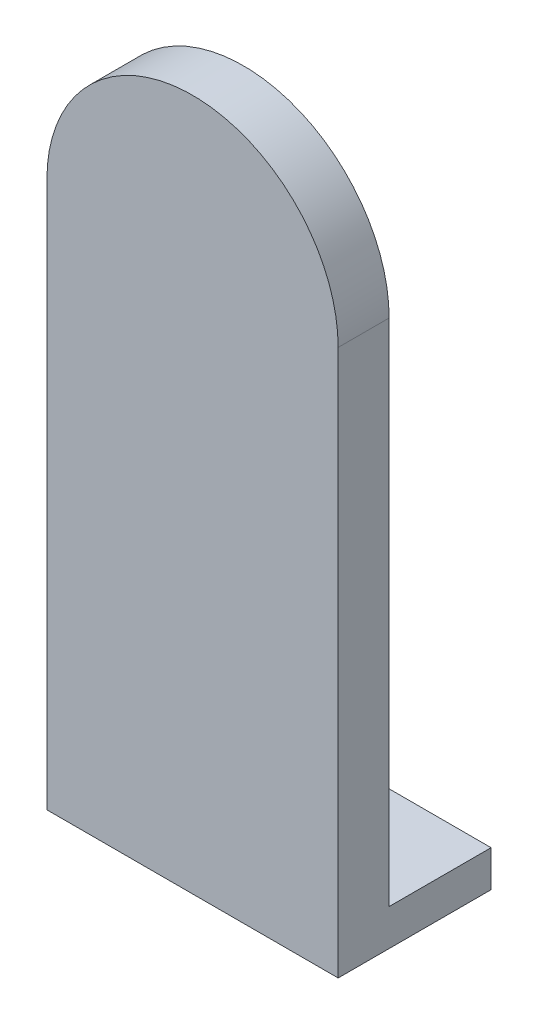
SolidWorks part; units mm, degrees
material "PBT General Purpose"
ref_plane "Front" through (0, 0, 0) normal (0, 0, 1) x (1, 0, 0)
ref_plane "Top" through (0, 0, 0) normal (0, 1, 0) x (1, 0, 0)
ref_plane "Right" through (0, 0, 0) normal (1, 0, 0) x (0, 0, -1)
sketch "Sketch1" plane through (0, 0, 0) normal (0, 0, 1) x (1, 0, 0)
  line L0 (0, 0) -> (0, -75) construction
  line L1 (20, 0) -> (20, -75)
  line L2 (-20, 0) -> (-20, -75)
  line L3 (-20, -75) -> (20, -75)
  arc A0 (20, 0) -> (-20, 0) centre (0, 0) ccw
  point P3 (0, -37.5)
  dimension "D1" = 40
  dimension "D2" = 75
extrude "Boss-Extrude1" add sketch "Sketch1" along normal blind 7
sketch "Sketch2" plane through (0, 0, 0) normal (0, 0, -1) x (-1, 0, 0)
  circle A0 centre (0, 0) radius 5
  dimension "D1" = 10
extrude "Boss-Extrude2" add sketch "Sketch2" along normal blind 4
sketch "Sketch3" plane through (0, 0, 0) normal (0, 0, -1) x (-1, 0, 0)
  line L0 (-20, -75) -> (-20, 0) construction
  line L1 (-20, -70) -> (20, -70)
  line L2 (-20, -70) -> (-20, -75)
  line L3 (-20, -75) -> (20, -75)
  line L4 (20, -70) -> (20, -75)
  dimension "D1" = 5
extrude "Boss-Extrude3" add sketch "Sketch3" along normal blind 14
sketch "Sketch5" plane through (0, -70, 0) normal (0, 1, 0) x (1, 0, 0)
  line L0 (10, 7) -> (-10, 7) construction
  line L1 (-10, 7) -> (0, 7) construction
  line L2 (0, 7) -> (0, 0) construction
  line L3 (-20, 0) -> (20, 0) construction
  line L4 (10, 7) -> (20, 7) construction
  line L5 (20, 14) -> (20, 0) construction
  circle A0 centre (10, 7) radius 1.5
  circle A1 centre (-10, 7) radius 1.5
  dimension "D1" = 3
  dimension "D2" = 20
extrude "Cut-Extrude1" cut sketch "Sketch5" against normal through all
